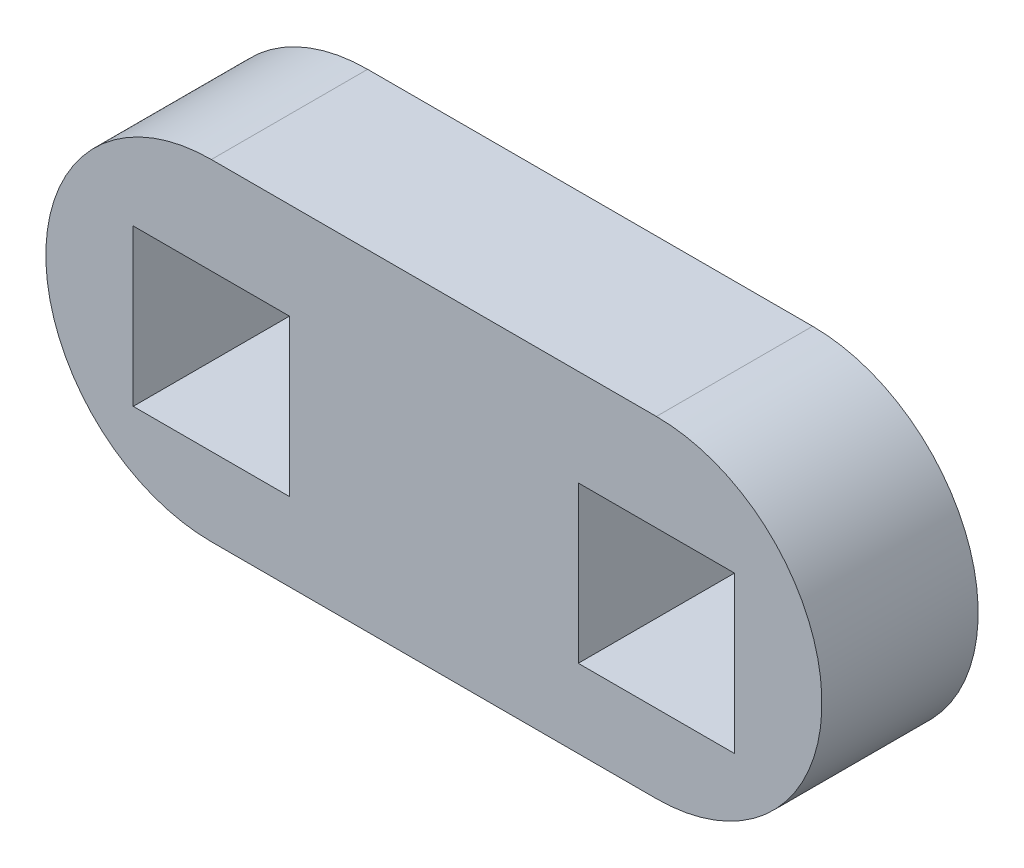
SolidWorks part; units mm, degrees
ref_plane "Front Plane" through (0, 0, 0) normal (0, 0, 1) x (1, 0, 0)
ref_plane "Top Plane" through (0, 0, 0) normal (0, 1, 0) x (1, 0, 0)
ref_plane "Right Plane" through (0, 0, 0) normal (1, 0, 0) x (0, 0, -1)
sketch "Sketch1" plane through (0, 0, 0) normal (0, 0, 1) x (1, 0, 0)
  line L0 (384.6105, 118.344) -> (367.5378, 118.344) construction
  line L1 (387.6077, 114.994) -> (381.6133, 114.994)
  line L2 (387.6077, 114.994) -> (387.6077, 120.9884)
  line L3 (387.6077, 120.9884) -> (381.6133, 120.9884)
  line L4 (381.6133, 114.994) -> (381.6133, 120.9884)
  line L5 (364.5406, 120.9884) -> (370.535, 120.9884)
  line L6 (364.5406, 120.9884) -> (364.5406, 114.994)
  line L7 (364.5406, 114.994) -> (370.535, 114.994)
  line L8 (370.535, 120.9884) -> (370.535, 114.994)
  line L9 (384.6105, 111.994) -> (367.5378, 111.994)
  line L10 (367.5378, 124.694) -> (384.6105, 124.694)
  arc A0 (384.6105, 111.994) -> (384.6105, 124.694) centre (384.6105, 118.344) ccw
  arc A1 (367.5378, 124.694) -> (367.5378, 111.994) centre (367.5378, 118.344) ccw
  point P10 (376.0742, 118.344)
extrude "Boss-Extrude1" add sketch "Sketch1" along normal blind 5.9944
